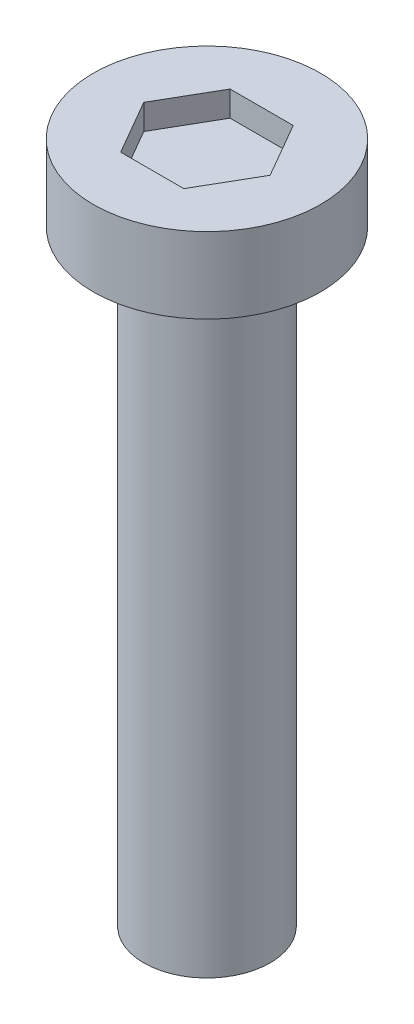
SolidWorks part; units mm, degrees
ref_plane "Front Plane" through (0, 0, 0) normal (0, 0, 1) x (1, 0, 0)
ref_plane "Top Plane" through (0, 0, 0) normal (0, 1, 0) x (1, 0, 0)
ref_plane "Right Plane" through (0, 0, 0) normal (1, 0, 0) x (0, 0, -1)
sketch "Sketch1" plane through (0, 0, 0) normal (0, 1, 0) x (1, 0, 0)
  circle A0 centre (0, 0) radius 1.25
  dimension "D1" = 2.5
extrude "Boss-Extrude1" add sketch "Sketch1" along normal blind 12
sketch "Sketch4" plane through (0, 12, 0) normal (0, 1, 0) x (1, 0, 0)
  circle A0 centre (0, 0) radius 2.25
  dimension "D1" = 4.5
extrude "Boss-Extrude2" add sketch "Sketch4" along normal blind 1.5
sketch "Sketch5" plane through (0, 13.5, 0) normal (0, 1, 0) x (1, 0, 0)
  line L1 (1.25, 0) -> (0.625, 1.0825)
  line L2 (0.625, 1.0825) -> (-0.625, 1.0825)
  line L3 (-0.625, 1.0825) -> (-1.25, 0)
  line L4 (-1.25, 0) -> (-0.625, -1.0825)
  line L5 (-0.625, -1.0825) -> (0.625, -1.0825)
  line L6 (0.625, -1.0825) -> (1.25, 0)
  circle A0 centre (0, 0) radius 1.0825 construction
  dimension "D1" = 1.25
extrude "Cut-Extrude1" cut sketch "Sketch5" against normal blind 0.5
thread "Thread1" pitch 0.7 start angle 0, offset 0, length 11, pitch 0.7, diameter 2.5
ref_plane "Plane1" through (1.25, 0, 0) normal (0, 0, 1) x (1, 0, 0)
sketch "Thread Profile1" plane through (1.25, 0, 0) normal (0, 0, 1) x (1, 0, 0)
  line L0 (0, 0) -> (0, 0.7) construction
  line L1 (0, 0) -> (0.3789, 0.2187)
  line L2 (0.3789, 0.2187) -> (0.3789, 0.3062)
  line L3 (0.3789, 0.3062) -> (0, 0.525)
  line L4 (0.3789, 0.2625) -> (0, 0.2625) construction
  line L11 (0, 0) -> (0, 0.525)
  point P2 (0, 0)
  dimension "Pitch" = 0.7
  dimension "Profile_Angle" = 60
  dimension "Profile_Land" = 0.0875
  dimension "Profile_Height" = 0.3789
